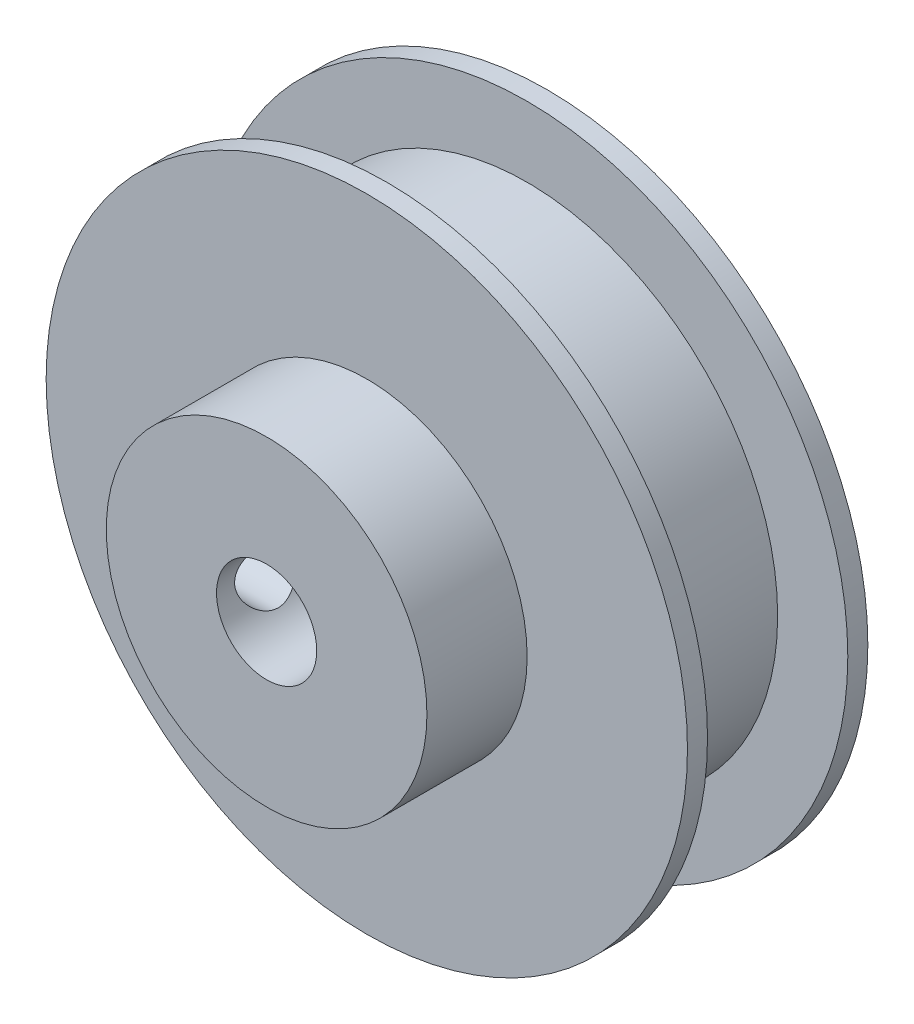
SolidWorks part; units mm, degrees
ref_plane "Plan de face" through (0, 0, 0) normal (0, 0, 1) x (1, 0, 0)
ref_plane "Plan de dessus" through (0, 0, 0) normal (0, 1, 0) x (1, 0, 0)
ref_plane "Plan de droite" through (0, 0, 0) normal (1, 0, 0) x (0, 0, -1)
sketch "Esquisse1" plane through (0, 0, 0) normal (0, 0, 1) x (1, 0, 0)
  circle A0 centre (0, 0) radius 16
  dimension "D1" = 32
extrude "Boss.-Extru.1" add sketch "Esquisse1" along normal blind 1
sketch "Esquisse2" plane through (0, 0, 1) normal (0, 0, 1) x (1, 0, 0)
  circle A0 centre (0, 0) radius 12.5
  dimension "D1" = 25
extrude "Boss.-Extru.2" add sketch "Esquisse2" along normal blind 7
sketch "Esquisse3" plane through (0, 0, 8) normal (0, 0, 1) x (1, 0, 0)
  circle A0 centre (0, 0) radius 16
extrude "Boss.-Extru.3" add sketch "Esquisse3" along normal blind 1
sketch "Esquisse4" plane through (0, 0, 9) normal (0, 0, 1) x (1, 0, 0)
  circle A0 centre (0, 0) radius 8
  dimension "D1" = 16
extrude "Boss.-Extru.4" add sketch "Esquisse4" along normal blind 5
sketch "Esquisse5" plane through (0, 0, 14) normal (0, 0, 1) x (1, 0, 0)
  circle A0 centre (0, 0) radius 2.5
  dimension "D1" = 5
extrude "Enlèv. mat.-Extru.1" cut sketch "Esquisse5" against normal through all
hole_wizard "Dégagement M31" positions "Esquisse3D3" profile "Esquisse7" hole size "M3" standard "Ansi Metric"
sketch3d "Esquisse3D3"
  line L0 (0, 0, 9) -> (0, 0, 13.9951) construction
  line L1 (0, 0, 14) -> (0, 0, 9) construction
  line L2 (0, 0, 11.4975) -> (-10.4119, 0, 11.4975) construction
  point P13 (0, 0, 11.4975)
  point P15 (0, 0, 11.4975)
  point P17 (0, 0, 9.9626)
  point P19 (-8, 0, 11.4975)
sketch "Esquisse7" plane through (-8, 0, 11.4975) normal (0, 1, 0) x (0, 0, 1)
  line L0 (0, 0) -> (0, 8)
  line L1 (0, 8) -> (1.6, 8)
  line L2 (1.6, 8) -> (1.6, 0.025)
  line L3 (1.6, 0.025) -> (1.625, 0)
  line L5 (1.625, 0) -> (0, 0)
  line L6 (-1.6, 0.025) -> (-1.625, 0) construction
  line L11 (0, -6.35) -> (0, 107.95) construction
  dimension "Diamètre du perçage jusqu'au prochain" = 3.2
  dimension "Profondeur du perçage jusqu'au prochain" = 8
  dimension "Diamètre du fraisage entrant" = 3.25
  dimension "Angle du fraisage entrant" = 90
